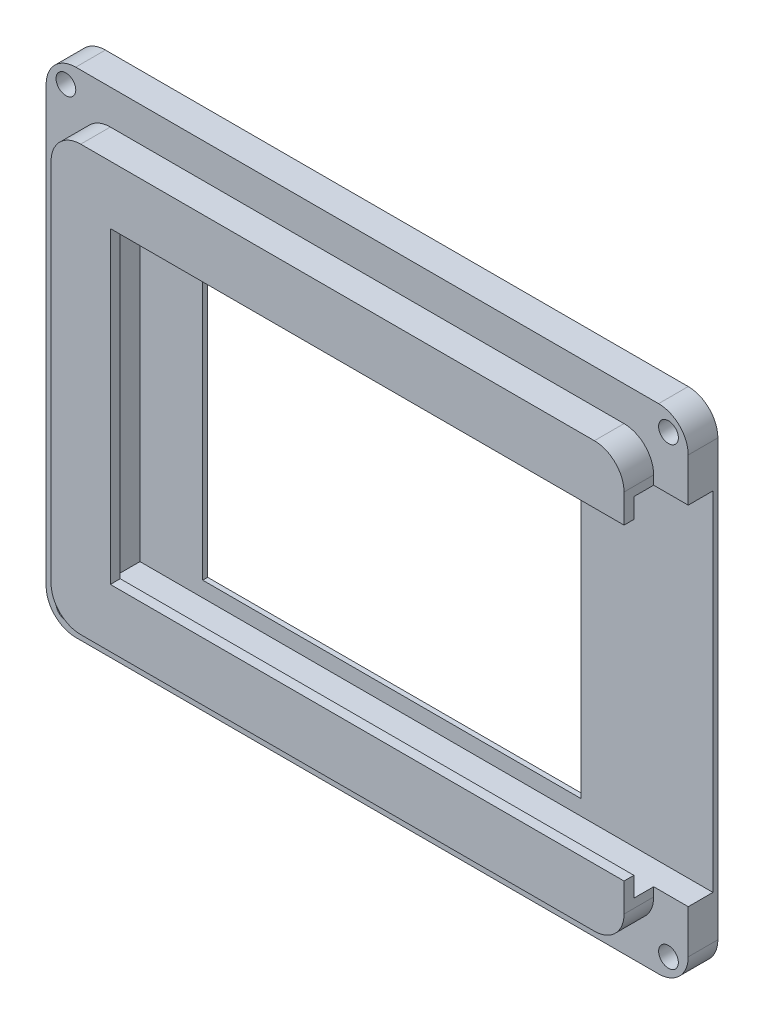
SolidWorks part; units mm, degrees
ref_plane "Ebene vorne" through (0, 0, 0) normal (0, 0, 1) x (1, 0, 0)
ref_plane "Ebene oben" through (0, 0, 0) normal (0, 1, 0) x (1, 0, 0)
ref_plane "Ebene rechts" through (0, 0, 0) normal (1, 0, 0) x (0, 0, -1)
sketch "Skizze1" plane through (0, 0, 0) normal (0, 0, 1) x (1, 0, 0)
  line L1 (0, 0) -> (65, 0)
  line L2 (0, 0) -> (0, -50)
  line L3 (0, -50) -> (65, -50)
  line L4 (65, 0) -> (65, -50)
  dimension "D1" = 50
  dimension "D2" = 65
extrude "Aufsatz-Linear austragen1" add sketch "Skizze1" along normal blind 3
sketch "Skizze2" plane through (0, 0, 3) normal (0, 0, 1) x (1, 0, 0)
  line L0 (3.5, -3.5) -> (3.5, -46.5)
  line L1 (0, 0) -> (65, 0)
  line L2 (0, 0) -> (0, -50)
  line L3 (0, -50) -> (65, -50)
  line L4 (65, 0) -> (65, -50)
  line L5 (3.5, -46.5) -> (61.5, -46.5)
  line L6 (61.5, -3.5) -> (61.5, -46.5)
  line L7 (3.5, -3.5) -> (61.5, -3.5)
  dimension "D1" = 3.5
extrude "Aufsatz-Linear austragen2" add sketch "Skizze2" along normal blind 3 contours L7 L0 L5 L6
sketch "Skizze7" plane through (65, -65, 0) normal (-1, 0, 0) x (0, 1, 0)
  line L1 (22.4, -0.5) -> (57.6, -0.5)
  line L2 (22.4, -0.5) -> (22.4, -5)
  line L3 (22.4, -5) -> (57.6, -5)
  line L4 (57.6, -0.5) -> (57.6, -5)
  line L8 (15, 0) -> (65, 0) construction
  point P9 (40, 0)
  dimension "D1" = 35.2
  dimension "D2" = 0.5
  dimension "D3" = 4.5
  dimension "D4" = 17.6
extrude "Schnitt-Linear austragen2" cut sketch "Skizze7" along normal blind 58
sketch "Skizze9" plane through (61.5, 0, 0) normal (1, 0, 0) x (0, 0, -1)
  line L0 (-5, -42.6) -> (-5, -7.4) construction
  line L1 (-5, -9.4) -> (-6, -9.4)
  line L2 (-5, -9.4) -> (-5, -40.6)
  line L3 (-5, -40.6) -> (-6, -40.6)
  line L4 (-6, -9.4) -> (-6, -40.6)
  line L5 (-6, -3.5) -> (-6, -46.5) construction
  line L6 (-5, -7.4) -> (-3, -7.4) construction
  line L7 (-0.5, -42.6) -> (-5, -42.6) construction
  dimension "D1" = 2
  dimension "D2" = 2
extrude "Schnitt-Linear austragen3" cut sketch "Skizze9" against normal blind 52
sketch "Skizze10" plane through (0, 0, 0) normal (0, 0, -1) x (-1, 0, 0)
  line L0 (-65, -7.4) -> (-65, -42.6) construction
  line L1 (-51.65, -8.95) -> (-13.35, -8.95)
  line L2 (-51.65, -8.95) -> (-51.65, -41.05)
  line L3 (-51.65, -41.05) -> (-13.35, -41.05)
  line L4 (-13.35, -8.95) -> (-13.35, -41.05)
  line L5 (-65, 0) -> (0, 0) construction
  point P4 (-65, -25)
  point P7 (-32.5, 0)
  dimension "D1" = 32.1
  dimension "D2" = 38.3
  dimension "D3" = 16.05
  dimension "D4" = 19.15
extrude "Schnitt-Linear austragen4" cut sketch "Skizze10" against normal up to next
fillet "Verrundung2" radius 3 8 edges at (61.5, -3.5, 4.5) (3.5, -3.5, 4.5) (3.5, -46.5, 4.5) (61.5, -46.5, 4.5) (65, -50, 1.5) (65, 0, 1.5) (0, 0, 1.5) (0, -50, 1.5)
sketch "Skizze11" plane through (0, 0, 0) normal (0, 0, -1) x (-1, 0, 0)
  line L0 (-3, -50) -> (-62, -50) construction
  line L1 (-65, -47) -> (-65, -3) construction
  line L3 (0, -3) -> (0, -47) construction
  line L4 (-62, 0) -> (-3, 0) construction
  circle A0 centre (-63, -2) radius 1
  circle A1 centre (-2, -2) radius 1
  circle A2 centre (-2, -48) radius 1
  circle A3 centre (-63, -48) radius 1
  dimension "D1" = 2
  dimension "D2" = 2
  dimension "D3" = 2
  dimension "D4" = 2
  dimension "D5" = 2
  dimension "D6" = 2
  dimension "D7" = 2
  dimension "D8" = 2
extrude "Schnitt-Linear austragen5" cut sketch "Skizze11" against normal through all
chamfer "Fase1" distance 0.5 angle 45 4 edges at (62, -48, 0) (1, -48, 0) (1, -2, 0) (62, -2, 0)
